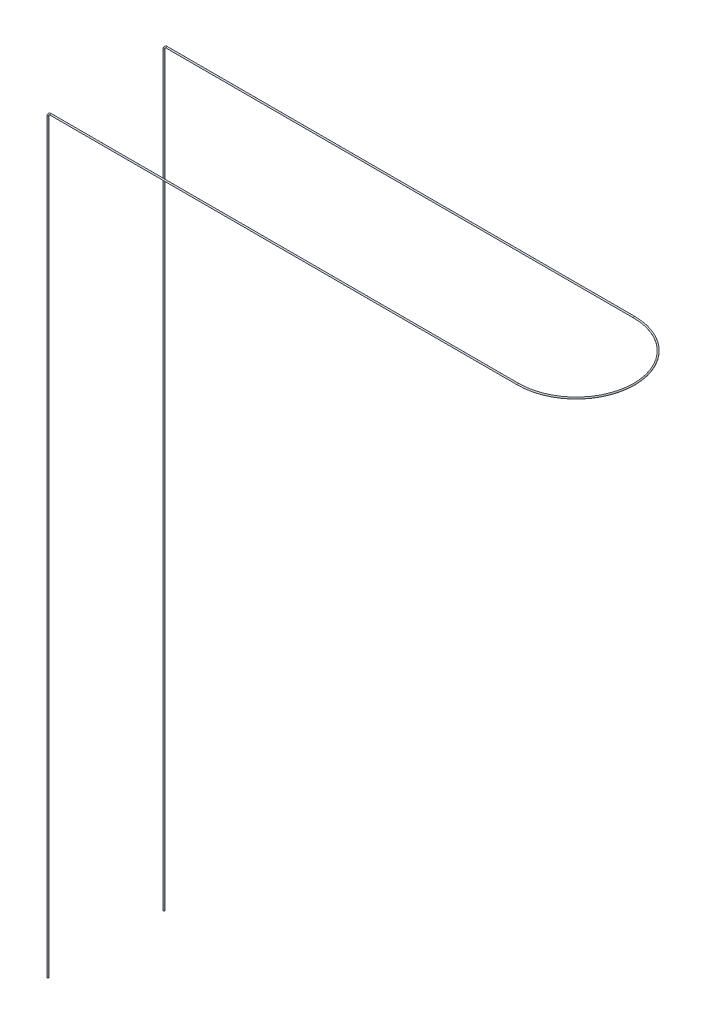
SolidWorks part; units mm, degrees
ref_plane "Plan de face" through (0, 0, 0) normal (0, 0, 1) x (1, 0, 0)
ref_plane "Plan de dessus" through (0, 0, 0) normal (0, 1, 0) x (1, 0, 0)
ref_plane "Plan de droite" through (0, 0, 0) normal (1, 0, 0) x (0, 0, -1)
sketch3d "Esquisse3D1"
  line L0 (0, 0, 0) -> (0, 257, 0)
  line L1 (1, 258, 0) -> (162, 258, 0)
  line L3 (162, 258, -40) -> (1, 258, -40)
  line L4 (0, 257, -40) -> (0, 0, -40)
  line L5 (0, 258, 0) -> (0, 258, -40) construction
  line L6 (0, 0, 0) -> (0, 0, -40) construction
  arc A0 (162, 258, -40) -> (162, 258, 0) centre (162, 258, -20) ccw
  arc A1 (1, 258, -40) -> (0, 257, -40) centre (1, 257, -40) ccw
  arc A2 (1, 258, 0) -> (0, 257, 0) centre (1, 257, 0) ccw
  point P4 (162, 238, -20)
  point P10 (0, 258, -40)
  point P12 (1, 257, -39)
  point P16 (0, 258, 0)
  point P18 (1, 257, 1)
  point P19 (0, 0, 0)
  dimension "D4" = 1
  dimension "D1" = 258
  dimension "D2" = 162
  dimension "D3" = 40
sweep "Balayage1" add path "Esquisse3D1" circular profile diameter 0.5 parameters "D3"=0.5
